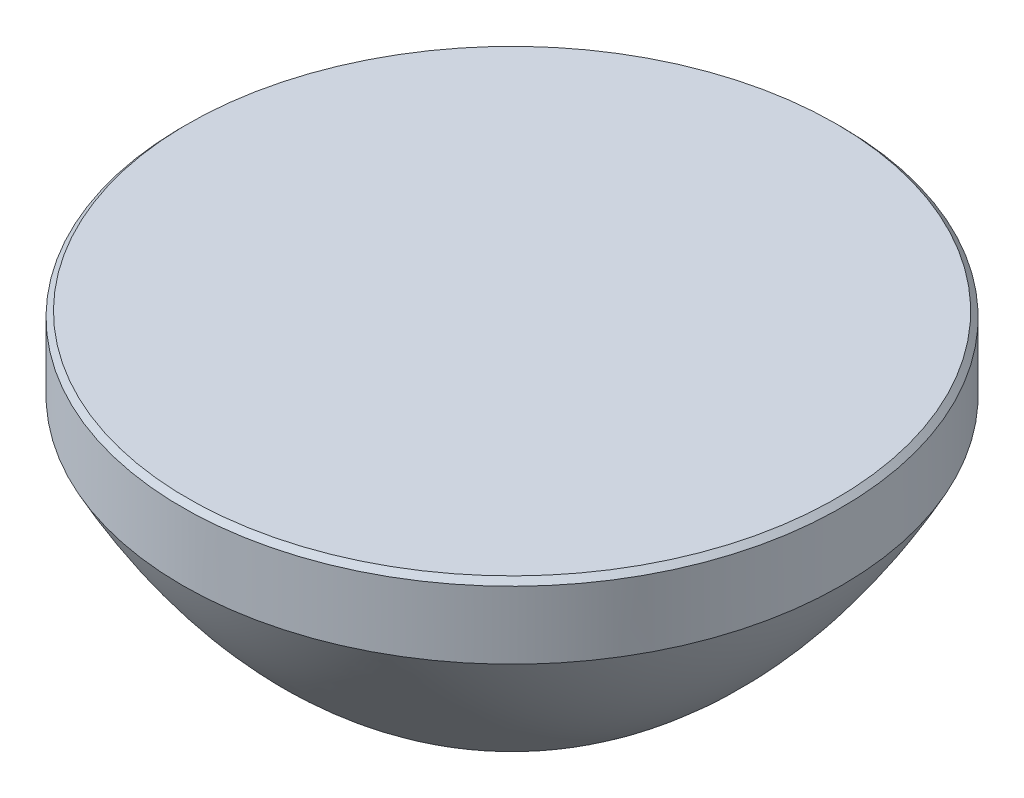
SolidWorks part; units mm, degrees
material "Glass"
ref_plane "Front Plane" through (0, 0, 0) normal (0, 0, 1) x (1, 0, 0)
ref_plane "Top Plane" through (0, 0, 0) normal (0, 1, 0) x (1, 0, 0)
ref_plane "Right Plane" through (0, 0, 0) normal (1, 0, 0) x (0, 0, -1)
sketch "Sketch1" plane through (0, 0, 0) normal (0, 0, 1) x (1, 0, 0)
  line L0 (12.3, 6) -> (0, 6)
  line L1 (0, 6) -> (0, -6)
  line L2 (12.5, 3.2393) -> (12.5, 5.8)
  line L3 (12.5, 5.8) -> (12.3, 6)
  line L4 (0, 6) -> (0, -6) construction
  ellipse E0 centre (-2.9311, 30.4949) end of major axis (-7.0289, 66.9222) minor radius 19.8724 (0, -6) -> (12.5, 3.2393) ccw
  point P3 (0, 0)
  point P4 (0, 0)
  point P5 (-7.0289, 66.9222)
  point P6 (0, -6)
  point P7 (12.5, 3.2393)
  point P8 (7.4783, -3.1389)
  point P9 (-13.3405, 64.1286)
  point P17 (0, 0)
  point P18 (13.2867, 25.0085)
  dimension "D1" = 12
  dimension "D2" = 12.5
  dimension "D3" = 2.7607
  dimension "D4" = 0.2
  dimension "D5" = 0.2
revolve "Revolve1" add sketch "Sketch1" angle 360 about L4
